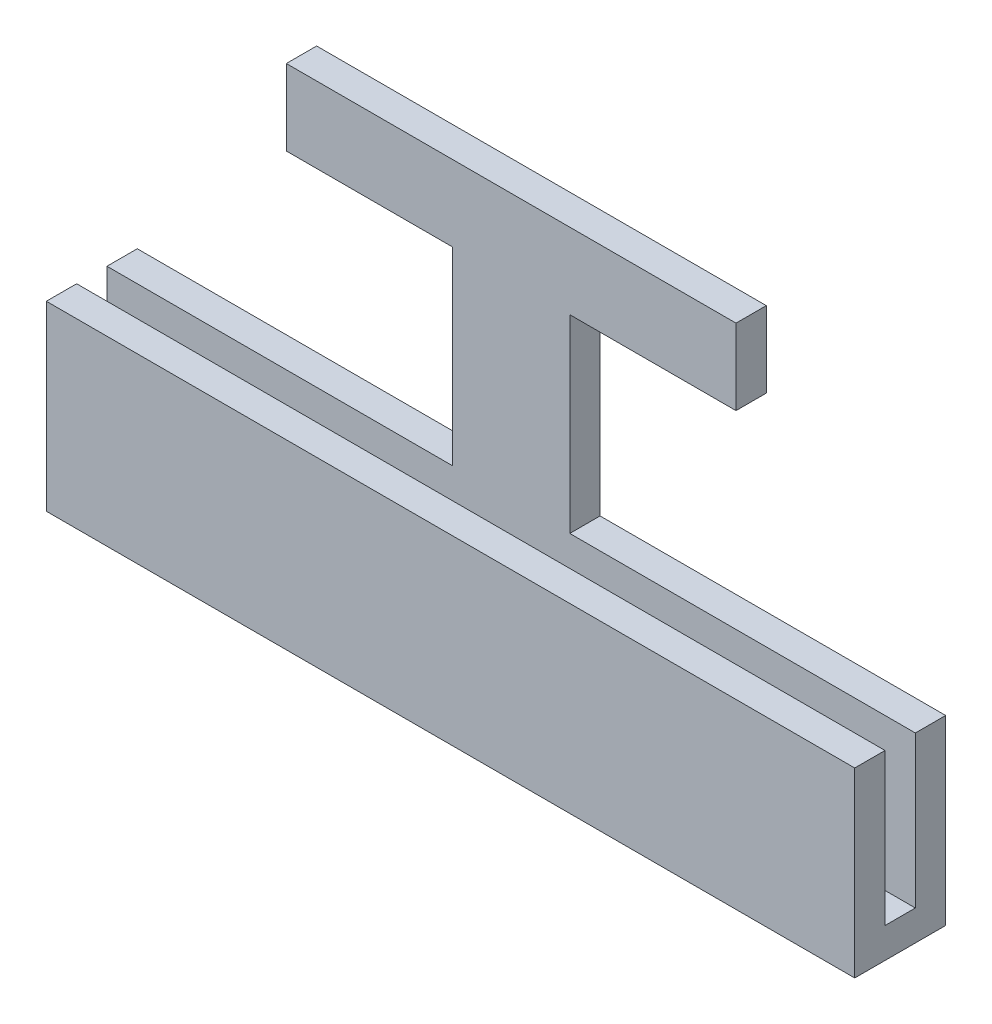
SolidWorks part; units mm, degrees
ref_plane "Ön Düzlem" through (0, 0, 0) normal (0, 0, 1) x (1, 0, 0)
ref_plane "Üst Düzlem" through (0, 0, 0) normal (0, 1, 0) x (1, 0, 0)
ref_plane "Sağ Düzlem" through (0, 0, 0) normal (1, 0, 0) x (0, 0, -1)
sketch "Sketch1" plane through (0, 0, 0) normal (0, 0, 1) x (1, 0, 0)
  line L2 (40, -7.5) -> (-40, -7.5)
  line L3 (40, -7.5) -> (40, 7.5)
  line L4 (40, 7.5) -> (-40, 7.5)
  line L5 (-40, -7.5) -> (-40, 7.5)
  line L6 (40, -7.5) -> (-40, 7.5) construction
  line L7 (40, 7.5) -> (-40, -7.5) construction
  dimension "D1" = 15
  dimension "D2" = 80
ref_plane "Plane1" through (0, -7.5, 0) normal (0, 1, 0) x (1, 0, 0)
sketch "Sketch2" plane through (0, -7.5, 0) normal (0, 1, 0) x (1, 0, 0)
  line L0 (0, 3) -> (0, 0) construction
  line L1 (-40, 0) -> (40, 0)
  line L2 (-40, 0) -> (-40, 3)
  line L3 (-40, 3) -> (40, 3)
  line L4 (40, 0) -> (40, 3)
  line L6 (40, -3) -> (-40, -3)
  line L7 (40, -3) -> (40, 6)
  line L8 (40, 6) -> (-40, 6)
  line L9 (-40, -3) -> (-40, 6)
  line L10 (40, -3) -> (-40, 6) construction
  line L11 (40, 6) -> (-40, -3) construction
  point P7 (0, 1.5)
  dimension "D1" = 80
  dimension "D2" = 3
  dimension "D3" = 9
  dimension "D4" = 80
ref_plane "Plane2" through (0, 0, -3) normal (0, 0, -1) x (-1, 0, 0)
sketch "Sketch3" plane through (0, 0, -3) normal (0, 0, -1) x (-1, 0, 0)
  line L1 (40, -7.5) -> (-40, -7.5)
  line L2 (40, -7.5) -> (40, 7.5)
  line L3 (40, 7.5) -> (5.8, 7.5)
  line L4 (-40, -7.5) -> (-40, 7.5)
  line L6 (22.25, 26.25) -> (5.8, 26.25)
  line L7 (22.25, 26.25) -> (22.25, 33.75)
  line L8 (22.25, 33.75) -> (-22.25, 33.75)
  line L9 (-22.25, 26.25) -> (-22.25, 33.75)
  line L10 (22.25, 26.25) -> (-22.25, 33.75) construction
  line L11 (22.25, 33.75) -> (-22.25, 26.25) construction
  line L12 (-5.8, 7.5) -> (-40, 7.5)
  line L14 (-5.8, 26.25) -> (-22.25, 26.25)
  line L16 (-5.8, 26.25) -> (-5.8, 7.5)
  line L18 (5.8, 26.25) -> (5.8, 7.5)
  point P5 (0, 30)
  dimension "D1" = 80
  dimension "D2" = 15
  dimension "D3" = 44.5
  dimension "D4" = 7.5
extrude "Boss-Extrude1" add sketch "Sketch1" along normal blind 3
extrude "Boss-Extrude2" add sketch "Sketch3" along normal blind 3 separate body
extrude "Boss-Extrude3" add sketch "Sketch2" against normal blind 3 contours L9 L3 L7 L8 | L1 L4 L3 L2 | L9 L6 L7 L1
